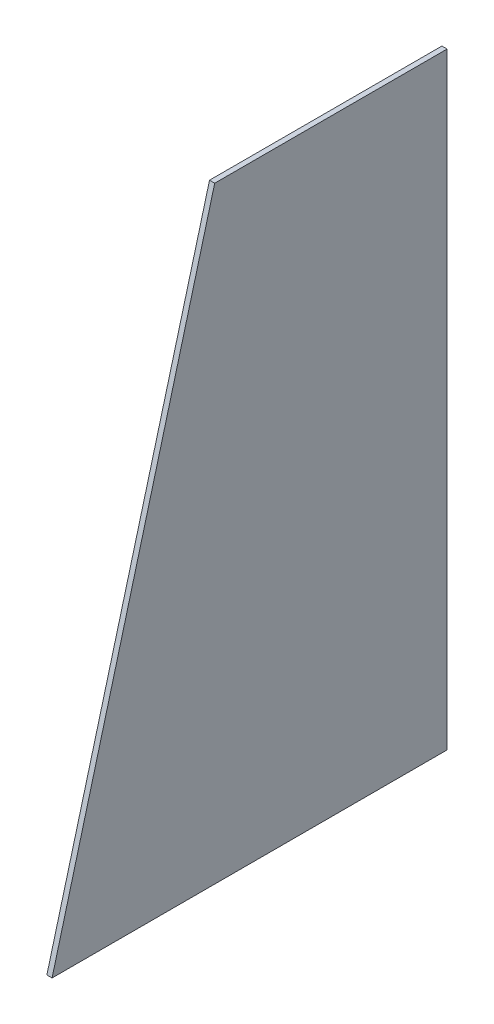
SolidWorks part; units mm, degrees
ref_plane "Front Plane" through (0, 0, 0) normal (0, 0, 1) x (1, 0, 0)
ref_plane "Top Plane" through (0, 0, 0) normal (0, 1, 0) x (1, 0, 0)
ref_plane "Right Plane" through (0, 0, 0) normal (1, 0, 0) x (0, 0, -1)
sketch "Sketch1" plane through (0, 0, 0) normal (1, 0, 0) x (0, 0, -1)
  line L0 (-20.1444, 175.2053) -> (111.0366, 175.2053)
  line L1 (111.0366, -175.2053) -> (-114.0366, -175.2053)
  line L2 (-114.0366, -175.2053) -> (-20.1444, 175.2053)
  line L3 (111.0366, 175.2053) -> (114.0366, 175.2053)
  line L4 (114.0366, 175.2053) -> (114.0366, -175.2053)
  line L5 (114.0366, -175.2053) -> (111.0366, -175.2053)
extrude "Boss-Extrude1" add sketch "Sketch1" along normal blind 3
